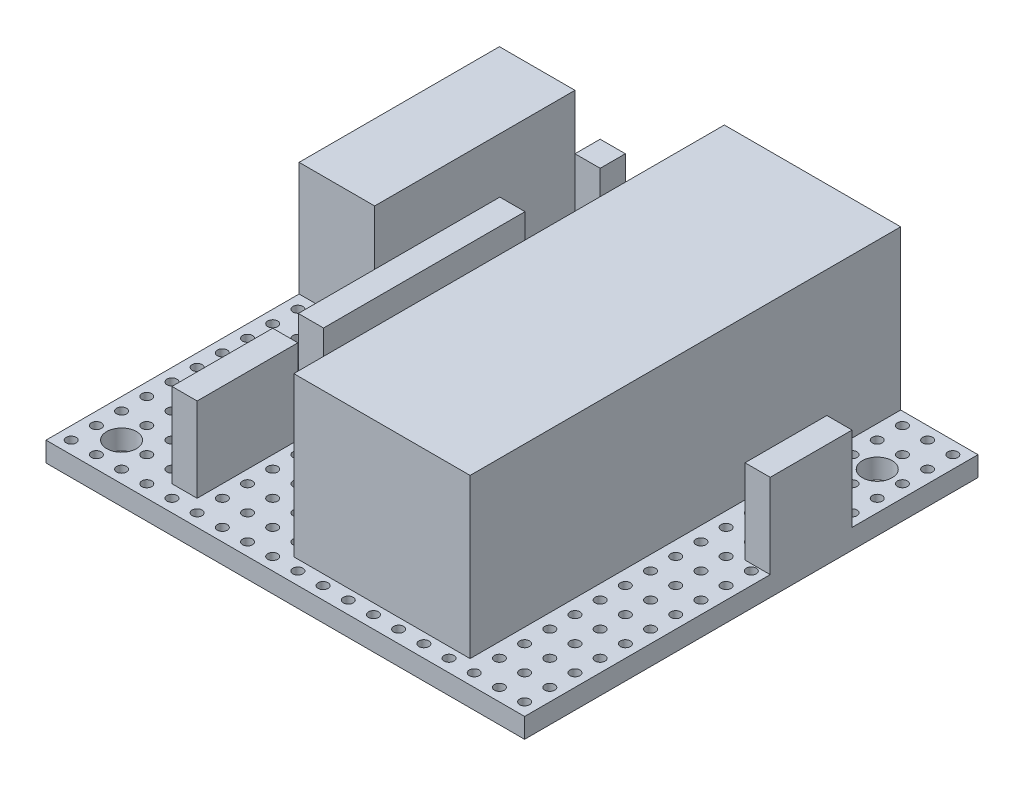
SolidWorks part; units mm, degrees
ref_plane "Front Plane" through (0, 0, 0) normal (0, 0, 1) x (1, 0, 0)
ref_plane "Top Plane" through (0, 0, 0) normal (0, 1, 0) x (1, 0, 0)
ref_plane "Right Plane" through (0, 0, 0) normal (1, 0, 0) x (0, 0, -1)
sketch "Sketch1" plane through (0, 0, 0) normal (0, 1, 0) x (1, 0, 0)
  line L1 (-28.6326, 15.7481) -> (34.8674, 15.7481)
  line L2 (-28.6326, 15.7481) -> (-28.6326, -29.9719)
  line L3 (-28.6326, -29.9719) -> (34.8674, -29.9719)
  line L4 (34.8674, 15.7481) -> (34.8674, -29.9719)
  circle A0 centre (33.5974, -28.7019) radius 0.5
  circle A1 centre (31.0574, -28.7019) radius 0.5
  circle A2 centre (28.5174, -28.7019) radius 0.5
  circle A3 centre (25.9774, -28.7019) radius 0.5
  circle A4 centre (23.4374, -28.7019) radius 0.5
  circle A5 centre (20.8974, -28.7019) radius 0.5
  circle A6 centre (18.3574, -28.7019) radius 0.5
  circle A7 centre (15.8174, -28.7019) radius 0.5
  circle A8 centre (13.2774, -28.7019) radius 0.5
  circle A9 centre (10.7374, -28.7019) radius 0.5
  circle A10 centre (8.1974, -28.7019) radius 0.5
  circle A11 centre (5.6574, -28.7019) radius 0.5
  circle A12 centre (3.1174, -28.7019) radius 0.5
  circle A13 centre (0.5774, -28.7019) radius 0.5
  circle A14 centre (-1.9626, -28.7019) radius 0.5
  circle A15 centre (-4.5026, -28.7019) radius 0.5
  circle A16 centre (-7.0426, -28.7019) radius 0.5
  circle A17 centre (-9.5826, -28.7019) radius 0.5
  circle A18 centre (-12.1226, -28.7019) radius 0.5
  circle A19 centre (-14.6626, -28.7019) radius 0.5
  circle A20 centre (-17.2026, -28.7019) radius 0.5
  circle A21 centre (-19.7426, -28.7019) radius 0.5
  circle A22 centre (-22.2826, -28.7019) radius 0.5
  circle A23 centre (-24.8226, -28.7019) radius 0.5
  circle A24 centre (-27.3626, -28.7019) radius 0.5
  circle A25 centre (31.0574, -26.1619) radius 0.5
  circle A26 centre (28.5174, -26.1619) radius 0.5
  circle A27 centre (25.9774, -26.1619) radius 0.5
  circle A28 centre (23.4374, -26.1619) radius 0.5
  circle A29 centre (20.8974, -26.1619) radius 0.5
  circle A30 centre (18.3574, -26.1619) radius 0.5
  circle A31 centre (15.8174, -26.1619) radius 0.5
  circle A32 centre (13.2774, -26.1619) radius 0.5
  circle A33 centre (10.7374, -26.1619) radius 0.5
  circle A34 centre (8.1974, -26.1619) radius 0.5
  circle A35 centre (5.6574, -26.1619) radius 0.5
  circle A36 centre (3.1174, -26.1619) radius 0.5
  circle A37 centre (0.5774, -26.1619) radius 0.5
  circle A38 centre (-1.9626, -26.1619) radius 0.5
  circle A39 centre (-4.5026, -26.1619) radius 0.5
  circle A40 centre (-7.0426, -26.1619) radius 0.5
  circle A41 centre (-9.5826, -26.1619) radius 0.5
  circle A42 centre (-12.1226, -26.1619) radius 0.5
  circle A43 centre (-14.6626, -26.1619) radius 0.5
  circle A44 centre (-17.2026, -26.1619) radius 0.5
  circle A45 centre (-19.7426, -26.1619) radius 0.5
  circle A46 centre (-22.2826, -26.1619) radius 0.5
  circle A47 centre (-24.8226, -26.1619) radius 0.5
  circle A48 centre (-27.3626, -26.1619) radius 0.5
  circle A49 centre (31.0574, -23.6219) radius 0.5
  circle A50 centre (28.5174, -23.6219) radius 0.5
  circle A51 centre (25.9774, -23.6219) radius 0.5
  circle A52 centre (23.4374, -23.6219) radius 0.5
  circle A53 centre (20.8974, -23.6219) radius 0.5
  circle A54 centre (18.3574, -23.6219) radius 0.5
  circle A55 centre (15.8174, -23.6219) radius 0.5
  circle A56 centre (13.2774, -23.6219) radius 0.5
  circle A57 centre (10.7374, -23.6219) radius 0.5
  circle A58 centre (8.1974, -23.6219) radius 0.5
  circle A59 centre (5.6574, -23.6219) radius 0.5
  circle A60 centre (3.1174, -23.6219) radius 0.5
  circle A61 centre (0.5774, -23.6219) radius 0.5
  circle A62 centre (-1.9626, -23.6219) radius 0.5
  circle A63 centre (-4.5026, -23.6219) radius 0.5
  circle A64 centre (-7.0426, -23.6219) radius 0.5
  circle A65 centre (-9.5826, -23.6219) radius 0.5
  circle A66 centre (-12.1226, -23.6219) radius 0.5
  circle A67 centre (-14.6626, -23.6219) radius 0.5
  circle A68 centre (-17.2026, -23.6219) radius 0.5
  circle A69 centre (-19.7426, -23.6219) radius 0.5
  circle A70 centre (-22.2826, -23.6219) radius 0.5
  circle A71 centre (-24.8226, -23.6219) radius 0.5
  circle A72 centre (-27.3626, -23.6219) radius 0.5
  circle A73 centre (31.0574, -21.0819) radius 0.5
  circle A74 centre (28.5174, -21.0819) radius 0.5
  circle A75 centre (25.9774, -21.0819) radius 0.5
  circle A76 centre (23.4374, -21.0819) radius 0.5
  circle A77 centre (20.8974, -21.0819) radius 0.5
  circle A78 centre (18.3574, -21.0819) radius 0.5
  circle A79 centre (15.8174, -21.0819) radius 0.5
  circle A80 centre (13.2774, -21.0819) radius 0.5
  circle A81 centre (10.7374, -21.0819) radius 0.5
  circle A82 centre (8.1974, -21.0819) radius 0.5
  circle A83 centre (5.6574, -21.0819) radius 0.5
  circle A84 centre (3.1174, -21.0819) radius 0.5
  circle A85 centre (0.5774, -21.0819) radius 0.5
  circle A86 centre (-1.9626, -21.0819) radius 0.5
  circle A87 centre (-4.5026, -21.0819) radius 0.5
  circle A88 centre (-7.0426, -21.0819) radius 0.5
  circle A89 centre (-9.5826, -21.0819) radius 0.5
  circle A90 centre (-12.1226, -21.0819) radius 0.5
  circle A91 centre (-14.6626, -21.0819) radius 0.5
  circle A92 centre (-17.2026, -21.0819) radius 0.5
  circle A93 centre (-19.7426, -21.0819) radius 0.5
  circle A94 centre (-22.2826, -21.0819) radius 0.5
  circle A95 centre (-24.8226, -21.0819) radius 0.5
  circle A96 centre (-27.3626, -21.0819) radius 0.5
  circle A97 centre (31.0574, -18.5419) radius 0.5
  circle A98 centre (28.5174, -18.5419) radius 0.5
  circle A99 centre (25.9774, -18.5419) radius 0.5
  circle A100 centre (23.4374, -18.5419) radius 0.5
  circle A101 centre (20.8974, -18.5419) radius 0.5
  circle A102 centre (18.3574, -18.5419) radius 0.5
  circle A103 centre (15.8174, -18.5419) radius 0.5
  circle A104 centre (13.2774, -18.5419) radius 0.5
  circle A105 centre (10.7374, -18.5419) radius 0.5
  circle A106 centre (8.1974, -18.5419) radius 0.5
  circle A107 centre (5.6574, -18.5419) radius 0.5
  circle A108 centre (3.1174, -18.5419) radius 0.5
  circle A109 centre (0.5774, -18.5419) radius 0.5
  circle A110 centre (-1.9626, -18.5419) radius 0.5
  circle A111 centre (-4.5026, -18.5419) radius 0.5
  circle A112 centre (-7.0426, -18.5419) radius 0.5
  circle A113 centre (-9.5826, -18.5419) radius 0.5
  circle A114 centre (-12.1226, -18.5419) radius 0.5
  circle A115 centre (-14.6626, -18.5419) radius 0.5
  circle A116 centre (-17.2026, -18.5419) radius 0.5
  circle A117 centre (-19.7426, -18.5419) radius 0.5
  circle A118 centre (-22.2826, -18.5419) radius 0.5
  circle A119 centre (-24.8226, -18.5419) radius 0.5
  circle A120 centre (-27.3626, -18.5419) radius 0.5
  circle A121 centre (31.0574, -16.0019) radius 0.5
  circle A122 centre (28.5174, -16.0019) radius 0.5
  circle A123 centre (25.9774, -16.0019) radius 0.5
  circle A124 centre (23.4374, -16.0019) radius 0.5
  circle A125 centre (20.8974, -16.0019) radius 0.5
  circle A126 centre (18.3574, -16.0019) radius 0.5
  circle A127 centre (15.8174, -16.0019) radius 0.5
  circle A128 centre (13.2774, -16.0019) radius 0.5
  circle A129 centre (10.7374, -16.0019) radius 0.5
  circle A130 centre (8.1974, -16.0019) radius 0.5
  circle A131 centre (5.6574, -16.0019) radius 0.5
  circle A132 centre (3.1174, -16.0019) radius 0.5
  circle A133 centre (0.5774, -16.0019) radius 0.5
  circle A134 centre (-1.9626, -16.0019) radius 0.5
  circle A135 centre (-4.5026, -16.0019) radius 0.5
  circle A136 centre (-7.0426, -16.0019) radius 0.5
  circle A137 centre (-9.5826, -16.0019) radius 0.5
  circle A138 centre (-12.1226, -16.0019) radius 0.5
  circle A139 centre (-14.6626, -16.0019) radius 0.5
  circle A140 centre (-17.2026, -16.0019) radius 0.5
  circle A141 centre (-19.7426, -16.0019) radius 0.5
  circle A142 centre (-22.2826, -16.0019) radius 0.5
  circle A143 centre (-24.8226, -16.0019) radius 0.5
  circle A144 centre (-27.3626, -16.0019) radius 0.5
  circle A145 centre (31.0574, -13.4619) radius 0.5
  circle A146 centre (28.5174, -13.4619) radius 0.5
  circle A147 centre (25.9774, -13.4619) radius 0.5
  circle A148 centre (23.4374, -13.4619) radius 0.5
  circle A149 centre (20.8974, -13.4619) radius 0.5
  circle A150 centre (18.3574, -13.4619) radius 0.5
  circle A151 centre (15.8174, -13.4619) radius 0.5
  circle A152 centre (13.2774, -13.4619) radius 0.5
  circle A153 centre (10.7374, -13.4619) radius 0.5
  circle A154 centre (8.1974, -13.4619) radius 0.5
  circle A155 centre (5.6574, -13.4619) radius 0.5
  circle A156 centre (3.1174, -13.4619) radius 0.5
  circle A157 centre (0.5774, -13.4619) radius 0.5
  circle A158 centre (-1.9626, -13.4619) radius 0.5
  circle A159 centre (-4.5026, -13.4619) radius 0.5
  circle A160 centre (-7.0426, -13.4619) radius 0.5
  circle A161 centre (-9.5826, -13.4619) radius 0.5
  circle A162 centre (-12.1226, -13.4619) radius 0.5
  circle A163 centre (-14.6626, -13.4619) radius 0.5
  circle A164 centre (-17.2026, -13.4619) radius 0.5
  circle A165 centre (-19.7426, -13.4619) radius 0.5
  circle A166 centre (-22.2826, -13.4619) radius 0.5
  circle A167 centre (-24.8226, -13.4619) radius 0.5
  circle A168 centre (-27.3626, -13.4619) radius 0.5
  circle A169 centre (31.0574, -10.9219) radius 0.5
  circle A170 centre (28.5174, -10.9219) radius 0.5
  circle A171 centre (25.9774, -10.9219) radius 0.5
  circle A172 centre (23.4374, -10.9219) radius 0.5
  circle A173 centre (20.8974, -10.9219) radius 0.5
  circle A174 centre (18.3574, -10.9219) radius 0.5
  circle A175 centre (15.8174, -10.9219) radius 0.5
  circle A176 centre (13.2774, -10.9219) radius 0.5
  circle A177 centre (10.7374, -10.9219) radius 0.5
  circle A178 centre (8.1974, -10.9219) radius 0.5
  circle A179 centre (5.6574, -10.9219) radius 0.5
  circle A180 centre (3.1174, -10.9219) radius 0.5
  circle A181 centre (0.5774, -10.9219) radius 0.5
  circle A182 centre (-1.9626, -10.9219) radius 0.5
  circle A183 centre (-4.5026, -10.9219) radius 0.5
  circle A184 centre (-7.0426, -10.9219) radius 0.5
  circle A185 centre (-9.5826, -10.9219) radius 0.5
  circle A186 centre (-12.1226, -10.9219) radius 0.5
  circle A187 centre (-14.6626, -10.9219) radius 0.5
  circle A188 centre (-17.2026, -10.9219) radius 0.5
  circle A189 centre (-19.7426, -10.9219) radius 0.5
  circle A190 centre (-22.2826, -10.9219) radius 0.5
  circle A191 centre (-24.8226, -10.9219) radius 0.5
  circle A192 centre (-27.3626, -10.9219) radius 0.5
  circle A193 centre (31.0574, -8.3819) radius 0.5
  circle A194 centre (28.5174, -8.3819) radius 0.5
  circle A195 centre (25.9774, -8.3819) radius 0.5
  circle A196 centre (23.4374, -8.3819) radius 0.5
  circle A197 centre (20.8974, -8.3819) radius 0.5
  circle A198 centre (18.3574, -8.3819) radius 0.5
  circle A199 centre (15.8174, -8.3819) radius 0.5
  circle A200 centre (13.2774, -8.3819) radius 0.5
  circle A201 centre (10.7374, -8.3819) radius 0.5
  circle A202 centre (8.1974, -8.3819) radius 0.5
  circle A203 centre (5.6574, -8.3819) radius 0.5
  circle A204 centre (3.1174, -8.3819) radius 0.5
  circle A205 centre (0.5774, -8.3819) radius 0.5
  circle A206 centre (-1.9626, -8.3819) radius 0.5
  circle A207 centre (-4.5026, -8.3819) radius 0.5
  circle A208 centre (-7.0426, -8.3819) radius 0.5
  circle A209 centre (-9.5826, -8.3819) radius 0.5
  circle A210 centre (-12.1226, -8.3819) radius 0.5
  circle A211 centre (-14.6626, -8.3819) radius 0.5
  circle A212 centre (-17.2026, -8.3819) radius 0.5
  circle A213 centre (-19.7426, -8.3819) radius 0.5
  circle A214 centre (-22.2826, -8.3819) radius 0.5
  circle A215 centre (-24.8226, -8.3819) radius 0.5
  circle A216 centre (-27.3626, -8.3819) radius 0.5
  circle A217 centre (31.0574, -5.8419) radius 0.5
  circle A218 centre (28.5174, -5.8419) radius 0.5
  circle A219 centre (25.9774, -5.8419) radius 0.5
  circle A220 centre (23.4374, -5.8419) radius 0.5
  circle A221 centre (20.8974, -5.8419) radius 0.5
  circle A222 centre (18.3574, -5.8419) radius 0.5
  circle A223 centre (15.8174, -5.8419) radius 0.5
  circle A224 centre (13.2774, -5.8419) radius 0.5
  circle A225 centre (10.7374, -5.8419) radius 0.5
  circle A226 centre (8.1974, -5.8419) radius 0.5
  circle A227 centre (5.6574, -5.8419) radius 0.5
  circle A228 centre (3.1174, -5.8419) radius 0.5
  circle A229 centre (0.5774, -5.8419) radius 0.5
  circle A230 centre (-1.9626, -5.8419) radius 0.5
  circle A231 centre (-4.5026, -5.8419) radius 0.5
  circle A232 centre (-7.0426, -5.8419) radius 0.5
  circle A233 centre (-9.5826, -5.8419) radius 0.5
  circle A234 centre (-12.1226, -5.8419) radius 0.5
  circle A235 centre (-14.6626, -5.8419) radius 0.5
  circle A236 centre (-17.2026, -5.8419) radius 0.5
  circle A237 centre (-19.7426, -5.8419) radius 0.5
  circle A238 centre (-22.2826, -5.8419) radius 0.5
  circle A239 centre (-24.8226, -5.8419) radius 0.5
  circle A240 centre (-27.3626, -5.8419) radius 0.5
  circle A241 centre (31.0574, -3.3019) radius 0.5
  circle A242 centre (28.5174, -3.3019) radius 0.5
  circle A243 centre (25.9774, -3.3019) radius 0.5
  circle A244 centre (23.4374, -3.3019) radius 0.5
  circle A245 centre (20.8974, -3.3019) radius 0.5
  circle A246 centre (18.3574, -3.3019) radius 0.5
  circle A247 centre (15.8174, -3.3019) radius 0.5
  circle A248 centre (13.2774, -3.3019) radius 0.5
  circle A249 centre (10.7374, -3.3019) radius 0.5
  circle A250 centre (8.1974, -3.3019) radius 0.5
  circle A251 centre (5.6574, -3.3019) radius 0.5
  circle A252 centre (3.1174, -3.3019) radius 0.5
  circle A253 centre (0.5774, -3.3019) radius 0.5
  circle A254 centre (-1.9626, -3.3019) radius 0.5
  circle A255 centre (-4.5026, -3.3019) radius 0.5
  circle A256 centre (-7.0426, -3.3019) radius 0.5
  circle A257 centre (-9.5826, -3.3019) radius 0.5
  circle A258 centre (-12.1226, -3.3019) radius 0.5
  circle A259 centre (-14.6626, -3.3019) radius 0.5
  circle A260 centre (-17.2026, -3.3019) radius 0.5
  circle A261 centre (-19.7426, -3.3019) radius 0.5
  circle A262 centre (-22.2826, -3.3019) radius 0.5
  circle A263 centre (-24.8226, -3.3019) radius 0.5
  circle A264 centre (-27.3626, -3.3019) radius 0.5
  circle A265 centre (31.0574, -0.7619) radius 0.5
  circle A266 centre (28.5174, -0.7619) radius 0.5
  circle A267 centre (25.9774, -0.7619) radius 0.5
  circle A268 centre (23.4374, -0.7619) radius 0.5
  circle A269 centre (20.8974, -0.7619) radius 0.5
  circle A270 centre (18.3574, -0.7619) radius 0.5
  circle A271 centre (15.8174, -0.7619) radius 0.5
  circle A272 centre (13.2774, -0.7619) radius 0.5
  circle A273 centre (10.7374, -0.7619) radius 0.5
  circle A274 centre (8.1974, -0.7619) radius 0.5
  circle A275 centre (5.6574, -0.7619) radius 0.5
  circle A276 centre (3.1174, -0.7619) radius 0.5
  circle A277 centre (0.5774, -0.7619) radius 0.5
  circle A278 centre (-1.9626, -0.7619) radius 0.5
  circle A279 centre (-4.5026, -0.7619) radius 0.5
  circle A280 centre (-7.0426, -0.7619) radius 0.5
  circle A281 centre (-9.5826, -0.7619) radius 0.5
  circle A282 centre (-12.1226, -0.7619) radius 0.5
  circle A283 centre (-14.6626, -0.7619) radius 0.5
  circle A284 centre (-17.2026, -0.7619) radius 0.5
  circle A285 centre (-19.7426, -0.7619) radius 0.5
  circle A286 centre (-22.2826, -0.7619) radius 0.5
  circle A287 centre (-24.8226, -0.7619) radius 0.5
  circle A288 centre (-27.3626, -0.7619) radius 0.5
  circle A289 centre (31.0574, 1.7781) radius 0.5
  circle A290 centre (28.5174, 1.7781) radius 0.5
  circle A291 centre (25.9774, 1.7781) radius 0.5
  circle A292 centre (23.4374, 1.7781) radius 0.5
  circle A293 centre (20.8974, 1.7781) radius 0.5
  circle A294 centre (18.3574, 1.7781) radius 0.5
  circle A295 centre (15.8174, 1.7781) radius 0.5
  circle A296 centre (13.2774, 1.7781) radius 0.5
  circle A297 centre (10.7374, 1.7781) radius 0.5
  circle A298 centre (8.1974, 1.7781) radius 0.5
  circle A299 centre (5.6574, 1.7781) radius 0.5
  circle A300 centre (3.1174, 1.7781) radius 0.5
  circle A301 centre (0.5774, 1.7781) radius 0.5
  circle A302 centre (-1.9626, 1.7781) radius 0.5
  circle A303 centre (-4.5026, 1.7781) radius 0.5
  circle A304 centre (-7.0426, 1.7781) radius 0.5
  circle A305 centre (-9.5826, 1.7781) radius 0.5
  circle A306 centre (-12.1226, 1.7781) radius 0.5
  circle A307 centre (-14.6626, 1.7781) radius 0.5
  circle A308 centre (-17.2026, 1.7781) radius 0.5
  circle A309 centre (-19.7426, 1.7781) radius 0.5
  circle A310 centre (-22.2826, 1.7781) radius 0.5
  circle A311 centre (-24.8226, 1.7781) radius 0.5
  circle A312 centre (-27.3626, 1.7781) radius 0.5
  circle A313 centre (31.0574, 4.3181) radius 0.5
  circle A314 centre (28.5174, 4.3181) radius 0.5
  circle A315 centre (25.9774, 4.3181) radius 0.5
  circle A316 centre (23.4374, 4.3181) radius 0.5
  circle A317 centre (20.8974, 4.3181) radius 0.5
  circle A318 centre (18.3574, 4.3181) radius 0.5
  circle A319 centre (15.8174, 4.3181) radius 0.5
  circle A320 centre (13.2774, 4.3181) radius 0.5
  circle A321 centre (10.7374, 4.3181) radius 0.5
  circle A322 centre (8.1974, 4.3181) radius 0.5
  circle A323 centre (5.6574, 4.3181) radius 0.5
  circle A324 centre (3.1174, 4.3181) radius 0.5
  circle A325 centre (0.5774, 4.3181) radius 0.5
  circle A326 centre (-1.9626, 4.3181) radius 0.5
  circle A327 centre (-4.5026, 4.3181) radius 0.5
  circle A328 centre (-7.0426, 4.3181) radius 0.5
  circle A329 centre (-9.5826, 4.3181) radius 0.5
  circle A330 centre (-12.1226, 4.3181) radius 0.5
  circle A331 centre (-14.6626, 4.3181) radius 0.5
  circle A332 centre (-17.2026, 4.3181) radius 0.5
  circle A333 centre (-19.7426, 4.3181) radius 0.5
  circle A334 centre (-22.2826, 4.3181) radius 0.5
  circle A335 centre (-24.8226, 4.3181) radius 0.5
  circle A336 centre (-27.3626, 4.3181) radius 0.5
  circle A337 centre (31.0574, 6.8581) radius 0.5
  circle A338 centre (28.5174, 6.8581) radius 0.5
  circle A339 centre (25.9774, 6.8581) radius 0.5
  circle A340 centre (23.4374, 6.8581) radius 0.5
  circle A341 centre (20.8974, 6.8581) radius 0.5
  circle A342 centre (18.3574, 6.8581) radius 0.5
  circle A343 centre (15.8174, 6.8581) radius 0.5
  circle A344 centre (13.2774, 6.8581) radius 0.5
  circle A345 centre (10.7374, 6.8581) radius 0.5
  circle A346 centre (8.1974, 6.8581) radius 0.5
  circle A347 centre (5.6574, 6.8581) radius 0.5
  circle A348 centre (3.1174, 6.8581) radius 0.5
  circle A349 centre (0.5774, 6.8581) radius 0.5
  circle A350 centre (-1.9626, 6.8581) radius 0.5
  circle A351 centre (-4.5026, 6.8581) radius 0.5
  circle A352 centre (-7.0426, 6.8581) radius 0.5
  circle A353 centre (-9.5826, 6.8581) radius 0.5
  circle A354 centre (-12.1226, 6.8581) radius 0.5
  circle A355 centre (-14.6626, 6.8581) radius 0.5
  circle A356 centre (-17.2026, 6.8581) radius 0.5
  circle A357 centre (-19.7426, 6.8581) radius 0.5
  circle A358 centre (-22.2826, 6.8581) radius 0.5
  circle A359 centre (-24.8226, 6.8581) radius 0.5
  circle A360 centre (-27.3626, 6.8581) radius 0.5
  circle A361 centre (31.0574, 9.3981) radius 0.5
  circle A362 centre (28.5174, 9.3981) radius 0.5
  circle A363 centre (25.9774, 9.3981) radius 0.5
  circle A364 centre (23.4374, 9.3981) radius 0.5
  circle A365 centre (20.8974, 9.3981) radius 0.5
  circle A366 centre (18.3574, 9.3981) radius 0.5
  circle A367 centre (15.8174, 9.3981) radius 0.5
  circle A368 centre (13.2774, 9.3981) radius 0.5
  circle A369 centre (10.7374, 9.3981) radius 0.5
  circle A370 centre (8.1974, 9.3981) radius 0.5
  circle A371 centre (5.6574, 9.3981) radius 0.5
  circle A372 centre (3.1174, 9.3981) radius 0.5
  circle A373 centre (0.5774, 9.3981) radius 0.5
  circle A374 centre (-1.9626, 9.3981) radius 0.5
  circle A375 centre (-4.5026, 9.3981) radius 0.5
  circle A376 centre (-7.0426, 9.3981) radius 0.5
  circle A377 centre (-9.5826, 9.3981) radius 0.5
  circle A378 centre (-12.1226, 9.3981) radius 0.5
  circle A379 centre (-14.6626, 9.3981) radius 0.5
  circle A380 centre (-17.2026, 9.3981) radius 0.5
  circle A381 centre (-19.7426, 9.3981) radius 0.5
  circle A382 centre (-22.2826, 9.3981) radius 0.5
  circle A383 centre (-24.8226, 9.3981) radius 0.5
  circle A384 centre (-27.3626, 9.3981) radius 0.5
  circle A385 centre (31.0574, 11.9381) radius 0.5
  circle A386 centre (28.5174, 11.9381) radius 0.5
  circle A387 centre (25.9774, 11.9381) radius 0.5
  circle A388 centre (23.4374, 11.9381) radius 0.5
  circle A389 centre (20.8974, 11.9381) radius 0.5
  circle A390 centre (18.3574, 11.9381) radius 0.5
  circle A391 centre (15.8174, 11.9381) radius 0.5
  circle A392 centre (13.2774, 11.9381) radius 0.5
  circle A393 centre (10.7374, 11.9381) radius 0.5
  circle A394 centre (8.1974, 11.9381) radius 0.5
  circle A395 centre (5.6574, 11.9381) radius 0.5
  circle A396 centre (3.1174, 11.9381) radius 0.5
  circle A397 centre (0.5774, 11.9381) radius 0.5
  circle A398 centre (-1.9626, 11.9381) radius 0.5
  circle A399 centre (-4.5026, 11.9381) radius 0.5
  circle A400 centre (-7.0426, 11.9381) radius 0.5
  circle A401 centre (-9.5826, 11.9381) radius 0.5
  circle A402 centre (-12.1226, 11.9381) radius 0.5
  circle A403 centre (-14.6626, 11.9381) radius 0.5
  circle A404 centre (-17.2026, 11.9381) radius 0.5
  circle A405 centre (-19.7426, 11.9381) radius 0.5
  circle A406 centre (-22.2826, 11.9381) radius 0.5
  circle A407 centre (-24.8226, 11.9381) radius 0.5
  circle A408 centre (-27.3626, 11.9381) radius 0.5
  circle A409 centre (33.5974, -26.1619) radius 0.5
  circle A410 centre (33.5974, -23.6219) radius 0.5
  circle A411 centre (33.5974, -21.0819) radius 0.5
  circle A412 centre (33.5974, -18.5419) radius 0.5
  circle A413 centre (33.5974, -16.0019) radius 0.5
  circle A414 centre (33.5974, -13.4619) radius 0.5
  circle A415 centre (33.5974, -10.9219) radius 0.5
  circle A416 centre (33.5974, -8.3819) radius 0.5
  circle A417 centre (33.5974, -5.8419) radius 0.5
  circle A418 centre (33.5974, -3.3019) radius 0.5
  circle A419 centre (33.5974, -0.7619) radius 0.5
  circle A420 centre (33.5974, 1.7781) radius 0.5
  circle A421 centre (33.5974, 4.3181) radius 0.5
  circle A422 centre (33.5974, 6.8581) radius 0.5
  circle A423 centre (33.5974, 9.3981) radius 0.5
  circle A424 centre (33.5974, 11.9381) radius 0.5
  circle A425 centre (33.5974, 14.4781) radius 0.5
  circle A426 centre (31.0574, 14.4781) radius 0.5
  circle A427 centre (28.5174, 14.4781) radius 0.5
  circle A428 centre (25.9774, 14.4781) radius 0.5
  circle A429 centre (23.4374, 14.4781) radius 0.5
  circle A430 centre (20.8974, 14.4781) radius 0.5
  circle A431 centre (18.3574, 14.4781) radius 0.5
  circle A432 centre (15.8174, 14.4781) radius 0.5
  circle A433 centre (13.2774, 14.4781) radius 0.5
  circle A434 centre (10.7374, 14.4781) radius 0.5
  circle A435 centre (8.1974, 14.4781) radius 0.5
  circle A436 centre (5.6574, 14.4781) radius 0.5
  circle A437 centre (3.1174, 14.4781) radius 0.5
  circle A438 centre (0.5774, 14.4781) radius 0.5
  circle A439 centre (-1.9626, 14.4781) radius 0.5
  circle A440 centre (-4.5026, 14.4781) radius 0.5
  circle A441 centre (-7.0426, 14.4781) radius 0.5
  circle A442 centre (-9.5826, 14.4781) radius 0.5
  circle A443 centre (-12.1226, 14.4781) radius 0.5
  circle A444 centre (-14.6626, 14.4781) radius 0.5
  circle A445 centre (-17.2026, 14.4781) radius 0.5
  circle A446 centre (-19.7426, 14.4781) radius 0.5
  circle A447 centre (-22.2826, 14.4781) radius 0.5
  circle A448 centre (-24.8226, 14.4781) radius 0.5
  circle A449 centre (-27.3626, 14.4781) radius 0.5
  dimension "D3" = 1
  dimension "D1" = 45.72
  dimension "D2" = 63.5
  dimension "D6" = 1.27
  dimension "D7" = 1.27
  dimension "D4" = 25
  dimension "D5" = 18
extrude "Boss-Extrude1" add sketch "Sketch1" along normal blind 2
sketch "Sketch4" plane through (0, 2, 0) normal (0, 1, 0) x (1, 0, 0)
  line L0 (-28.6326, -29.9719) -> (34.8674, -29.9719) construction
  line L1 (34.8674, 15.7481) -> (19.6274, 15.7481)
  line L2 (34.8674, 15.7481) -> (34.8674, -29.9719)
  line L3 (34.8674, -29.9719) -> (19.6274, -29.9719)
  line L4 (19.6274, 15.7481) -> (19.6274, -29.9719)
  dimension "D1" = 15.24
extrude "Cut-Extrude1" cut sketch "Sketch4" against normal through all both and the other way through all
sketch "Sketch2" plane through (0, 2, 0) normal (0, 1, 0) x (1, 0, 0)
  line L0 (19.6274, 15.7481) -> (-28.6326, 15.7481) construction
  line L1 (11.8312, -27.6709) -> (-5.9488, -27.6709)
  line L2 (11.8312, -27.6709) -> (11.8312, 15.7481)
  line L3 (11.8312, 15.7481) -> (-5.9488, 15.7481)
  line L4 (-5.9488, -27.6709) -> (-5.9488, 15.7481)
  dimension "D1" = 17.78
extrude "Boss-Extrude2" add sketch "Sketch2" along normal blind 16
sketch "Sketch3" plane through (0, 2, 0) normal (0, 1, 0) x (1, 0, 0)
  line L1 (-28.6326, 15.7481) -> (-21.0126, 15.7481)
  line L2 (-28.6326, 15.7481) -> (-28.6326, -4.4519)
  line L3 (-28.6326, -4.4519) -> (-21.0126, -4.4519)
  line L4 (-21.0126, 15.7481) -> (-21.0126, -4.4519)
  dimension "D1" = 7.62
  dimension "D2" = 20.2
extrude "Boss-Extrude3" add sketch "Sketch3" along normal blind 11.5
sketch "Sketch5" plane through (0, 2, 0) normal (0, 1, 0) x (1, 0, 0)
  circle A0 centre (-24.8226, -26.1619) radius 1.5
  circle A1 centre (15.8174, 9.3981) radius 1.5
  circle A4 centre (-17.2026, 9.3981) radius 1.5
  dimension "D1" = 3
extrude "Cut-Extrude2" cut sketch "Sketch5" against normal through all both and the other way through all
sketch "Sketch6" plane through (0, 2, 0) normal (0, 1, 0) x (1, 0, 0)
  line L0 (-28.6326, -4.4519) -> (-28.6326, -29.9719) construction
  line L1 (-15.9326, -27.4319) -> (-18.4726, -27.4319)
  line L2 (-15.9326, -27.4319) -> (-15.9326, -17.2719)
  line L3 (-15.9326, -17.2719) -> (-18.4726, -17.2719)
  line L4 (-18.4726, -27.4319) -> (-18.4726, -17.2719)
  line L5 (-28.6326, -29.9719) -> (19.6274, -29.9719) construction
  line L6 (-5.9488, 15.7481) -> (-21.0126, 15.7481) construction
  line L7 (-15.9326, -14.6887) -> (-18.4726, -14.6887)
  line L8 (-15.9326, -14.6887) -> (-15.9326, 5.6313)
  line L9 (-15.9326, 5.6313) -> (-18.4726, 5.6313)
  line L10 (-18.4726, -14.6887) -> (-18.4726, 5.6313)
  line L11 (-15.9326, 15.7481) -> (-18.4726, 15.7481)
  line L12 (-15.9326, 15.7481) -> (-15.9326, 13.2081)
  line L13 (-15.9326, 13.2081) -> (-18.4726, 13.2081)
  line L14 (-18.4726, 15.7481) -> (-18.4726, 13.2081)
  line L15 (19.6274, 15.7481) -> (19.6274, -29.9719) construction
  line L16 (19.6274, 3.0481) -> (17.0874, 3.0481)
  line L17 (19.6274, 3.0481) -> (19.6274, -5.2052)
  line L18 (19.6274, -5.2052) -> (17.0874, -5.2052)
  line L19 (17.0874, 3.0481) -> (17.0874, -5.2052)
  line L20 (19.6274, 15.7481) -> (11.8312, 15.7481) construction
  dimension "D1" = 2.54
  dimension "D2" = 10.16
  dimension "D3" = 10.16
  dimension "D4" = 2.54
  dimension "D5" = 20.32
  dimension "D6" = 2.54
  dimension "D7" = 12.7
  dimension "D8" = 2.54
extrude "Boss-Extrude4" add sketch "Sketch6" along normal blind 8.5
